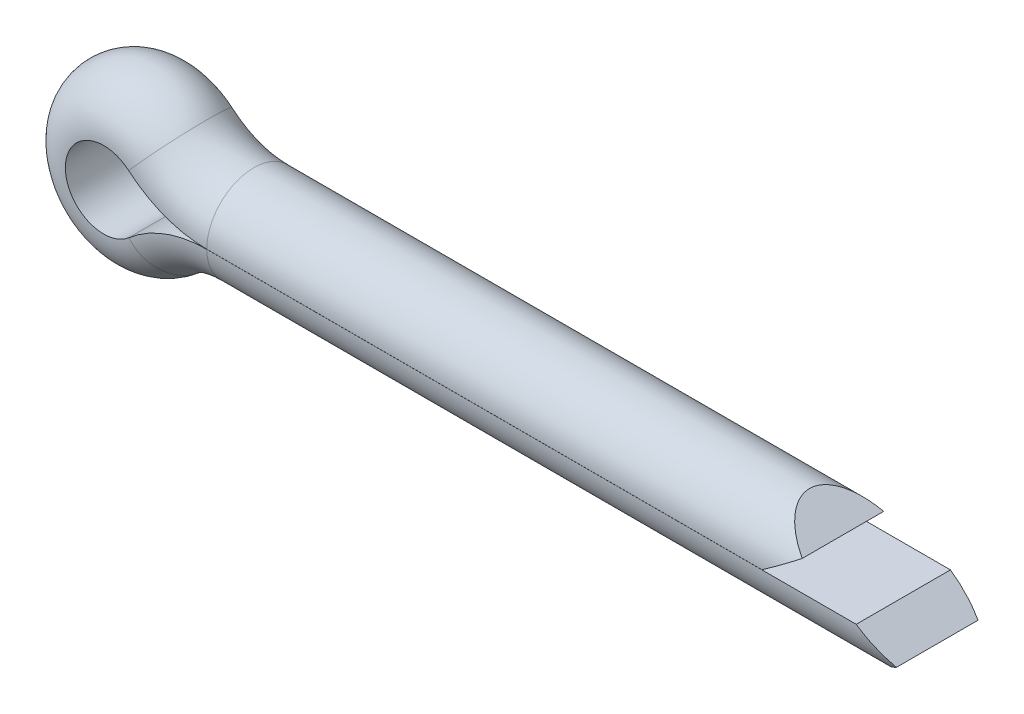
SolidWorks part; units mm, degrees
material "Q215"
ref_plane "Front" through (0, 0, 0) normal (0, 0, 1) x (1, 0, 0)
ref_plane "Top" through (0, 0, 0) normal (0, 1, 0) x (1, 0, 0)
ref_plane "Right" through (0, 0, 0) normal (1, 0, 0) x (0, 0, -1)
sketch "草图2" plane through (0, 0, 0) normal (0, 0, 1) x (1, 0, 0)
  line L0 (20, 1.6) -> (0, 1.6)
  line L1 (0, -1.6) -> (23.2, -1.6)
  line L2 (0, 0) -> (49.7718, 0) construction
  line L3 (0, 0) -> (0, 16.5256) construction
  line L4 (-6.4, 0) -> (-6.4, 14.2137) construction
  arc A0 (0, 1.6) -> (-1.6069, 2.1968) centre (0, 4.0615) cw
  arc A1 (-1.6069, 2.1968) -> (-1.6069, -2.1968) centre (-3.5, 0) ccw
  arc A2 (-1.6069, -2.1968) -> (0, -1.6) centre (0, -4.0615) cw
ref_plane "SectionPlane" through (20, 0, 0) normal (1, 0, 0) x (0, 0, -1)
sketch "草图1" plane through (20, 0, 0) normal (1, 0, 0) x (0, 0, -1)
  line L1 (-1.6, 0.002) -> (1.6, 0.002)
  arc A0 (1.6, 0.002) -> (-1.6, 0.002) centre (0, 0) ccw
sweep "Body" add profiles "草图1" path "草图2"
sketch "草图3" plane through (0, 0, 0) normal (0, 0, 1) x (1, 0, 0)
  line L0 (0, 0) -> (0, 16.2682) construction
  line L1 (0, 0) -> (75.9079, 0) construction
  line L2 (0, 0) -> (23.2, 0) construction
  line L3 (20, 0.801) -> (18.8531, 1.61)
  line L4 (20, 0.002) -> (20, 1.6) construction
  line L6 (20, 0.801) -> (18.8475, 0)
  line L7 (23.2, -0.801) -> (22.0475, 0)
  line L8 (23.2, -1.6) -> (23.2, -0.002) construction
  line L9 (23.2, -0.801) -> (22.0531, -1.61)
  line L10 (22.0475, 0) -> (18.8475, 0)
  line L11 (18.8531, 1.61) -> (23.21, 1.61)
  line L12 (23.21, 1.61) -> (23.21, -1.61)
  line L13 (23.21, -1.61) -> (22.0531, -1.61)
  line L14 (20, 1.6) -> (0, 1.6) construction
  dimension "D1" = 0.01
  dimension "D2" = 0.01
  dimension "D3" = 70
  dimension "D4" = 70
extrude "ConeCut" cut sketch "草图3" against normal through all and the other way through all
equation "' \"Diameter@草图2\" = 9.5"
equation "' \"c@草图2\" = 19"
equation "' \"b@草图2\" = 20"
equation "' \"a@草图2\" = 6.3"
equation "' \"l@草图2\" = 45"
equation "' \"Diameter@草图2\" = 1"
equation "' \"c@草图2\" = 2"
equation "' \"b@草图2\" = 3"
equation "' \"a@草图2\" = 2.5"
equation "' \"l@草图2\" = 8"
equation "' \"Diameter@草图2\" = 0.5"
equation "' \"c@草图2\" = 1"
equation "' \"b@草图2\" = 2"
equation "' \"a@草图2\" = 1.6"
equation "' \"l@草图2\" = 4"
equation "\"Diameter@草图1\" = \"Diameter@草图2\""
equation "\"Length@SectionPlane\" = \"l@草图2\""
